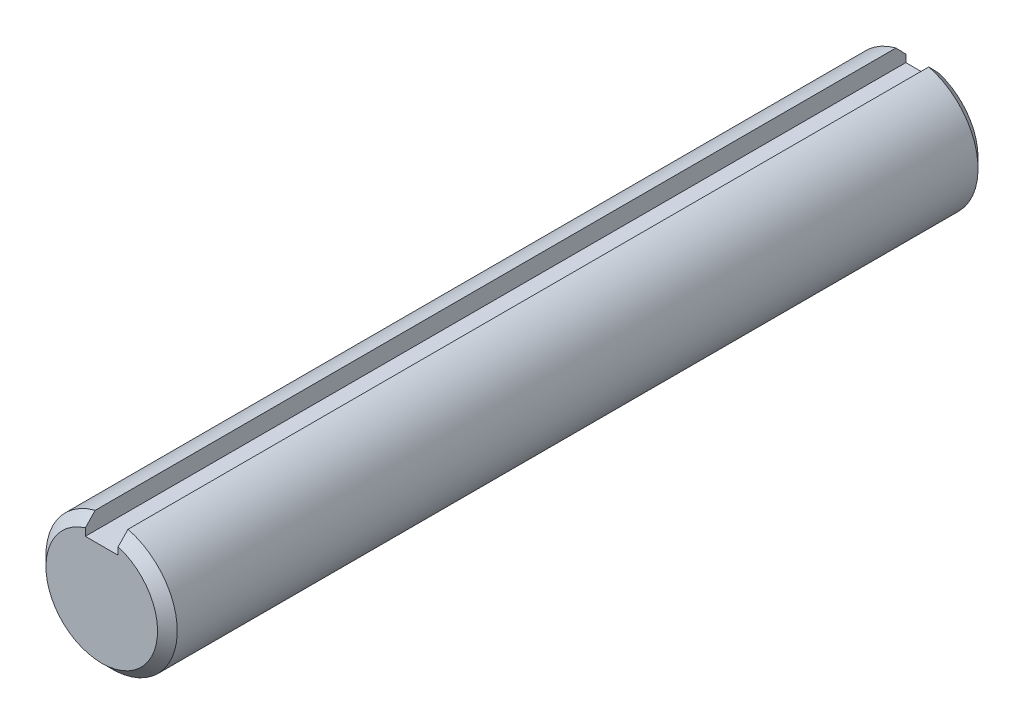
SolidWorks part; units mm, degrees
ref_plane "Front" through (0, 0, 0) normal (0, 0, 1) x (1, 0, 0)
ref_plane "Top" through (0, 0, 0) normal (0, 1, 0) x (1, 0, 0)
ref_plane "Right" through (0, 0, 0) normal (1, 0, 0) x (0, 0, -1)
sketch "Sketch1" plane through (0, 0, 0) normal (0, 0, 1) x (1, 0, 0)
  circle A0 centre (0, 0) radius 4
  dimension "dia" = 8
extrude "Extrude1" add sketch "Sketch1" along normal mid plane 50
sketch "Sketch2" plane through (0, 0, 0) normal (1, 0, 0) x (0, 0, -1)
  point P0 (-25, 4)
  point P1 (25, 4)
  point P2 (25, -4)
chamfer "Chamfer1" distance 0.6 angle 45 2 edges at (4, 0, -25) (4, 0, 25)
sketch "Sketch3" plane through (0, 0, 0) normal (0, 0, 1) x (1, 0, 0)
  line L1 (-1, 4) -> (1, 4)
  line L2 (-1, 4) -> (-1, 2.8)
  line L3 (-1, 2.8) -> (1, 2.8)
  line L4 (1, 4) -> (1, 2.8)
  dimension "key wd" = 2
  dimension "key dp" = 1.2
extrude "Extrude2" cut sketch "Sketch3" against normal through all and the other way through all
equation "\"D1@Chamfer1\" = \"dia@Sketch1\" * .075"
